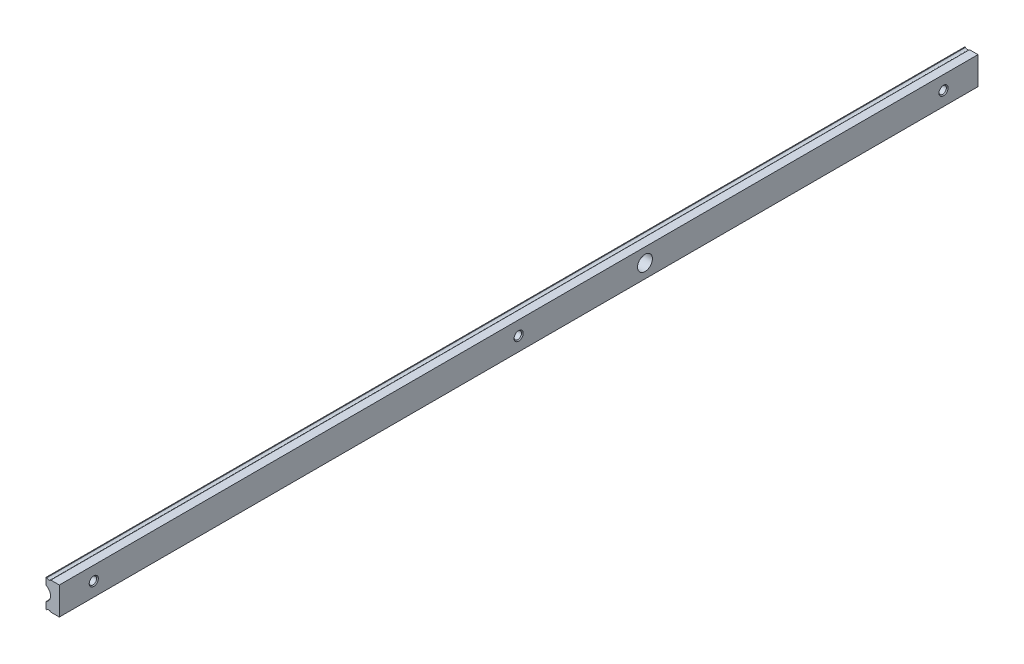
SolidWorks part; units mm, degrees
ref_plane "Front Plane" through (0, 0, 0) normal (0, 0, 1) x (1, 0, 0)
ref_plane "Top Plane" through (0, 0, 0) normal (0, 1, 0) x (1, 0, 0)
ref_plane "Right Plane" through (0, 0, 0) normal (1, 0, 0) x (0, 0, -1)
ref_plane "Plane1" through (0, 0, 0) normal (0, 0, 1) x (1, 0, 0)
sketch "Sketch1" plane through (0, 0, 0) normal (0, 0, 1) x (1, 0, 0)
  line L0 (0, 2.9747) -> (0, 0)
  line L1 (0, 0) -> (0.3056, 0)
  line L2 (2.0944, 0) -> (5.8, 0)
  line L3 (5.8, 0) -> (5.8, 12.1)
  line L4 (5.8, 12.1) -> (2.0944, 12.1)
  line L5 (0.3056, 12.1) -> (0, 12.1)
  line L6 (0, 12.1) -> (0, 9.1253)
  arc A0 (0.3056, 0) -> (2.0944, 0) centre (1.2, -0.8) cw
  arc A1 (2.0944, 12.1) -> (0.3056, 12.1) centre (1.2, 12.9) cw
  arc A2 (0, 9.1253) -> (0, 2.9747) centre (-1.45, 6.05) cw
extrude "Boss-Extrude1" add sketch "Sketch1" along normal blind 400
ref_plane "Plane2" through (0, 0, 15) normal (0, 0, 1) x (1, 0, 0)
sketch "Sketch2" plane through (0, 0, 15) normal (0, 0, 1) x (1, 0, 0)
  line L0 (1.2995, 6.05) -> (1.2995, 8.05)
  line L1 (1.2995, 8.05) -> (1.6785, 7.671)
  line L2 (1.6785, 7.671) -> (5.421, 7.671)
  line L3 (5.421, 7.671) -> (5.8, 8.05)
  line L4 (5.8, 8.05) -> (5.8, 6.05)
  line L5 (5.8, 6.05) -> (1.2995, 6.05)
  line L6 (5.8, 6.05) -> (0, 6.05) construction
revolve "Cut-Revolve1" cut sketch "Sketch2" angle 360 about L6
cosmetic thread "Cosmetic Thread1" parameters "D1"=4.1215, "D2"=4
ref_plane "Plane3" through (0, 0, 385) normal (0, 0, 1) x (1, 0, 0)
sketch "Sketch3" plane through (0, 0, 385) normal (0, 0, 1) x (1, 0, 0)
  line L0 (1.2995, 6.05) -> (1.2995, 8.05)
  line L1 (1.2995, 8.05) -> (1.6785, 7.671)
  line L2 (1.6785, 7.671) -> (5.421, 7.671)
  line L3 (5.421, 7.671) -> (5.8, 8.05)
  line L4 (5.8, 8.05) -> (5.8, 6.05)
  line L5 (5.8, 6.05) -> (1.2995, 6.05)
  line L6 (5.8, 6.05) -> (0, 6.05) construction
revolve "Cut-Revolve2" cut sketch "Sketch3" angle 360 about L6
cosmetic thread "Cosmetic Thread2" parameters "D1"=4.1215, "D2"=4
ref_plane "Plane4" through (0, 0, 200) normal (0, 0, 1) x (1, 0, 0)
sketch "Sketch4" plane through (0, 0, 200) normal (0, 0, 1) x (1, 0, 0)
  line L0 (1.2995, 6.05) -> (1.2995, 8.05)
  line L1 (1.2995, 8.05) -> (1.6785, 7.671)
  line L2 (1.6785, 7.671) -> (5.421, 7.671)
  line L3 (5.421, 7.671) -> (5.8, 8.05)
  line L4 (5.8, 8.05) -> (5.8, 6.05)
  line L5 (5.8, 6.05) -> (1.2995, 6.05)
  line L6 (5.8, 6.05) -> (0, 6.05) construction
revolve "Cut-Revolve3" cut sketch "Sketch4" angle 360 about L6
cosmetic thread "Cosmetic Thread3" parameters "D1"=4.1215, "D2"=4
ref_plane "Plane5" through (5.8, 0, 0) normal (1, 0, 0) x (0, 0, -1)
sketch "Sketch5" plane through (5.8, 0, 0) normal (1, 0, 0) x (0, 0, -1)
  circle A0 centre (-145, 6.05) radius 3.25
extrude "Cut-Extrude1" cut sketch "Sketch5" against normal blind 6
